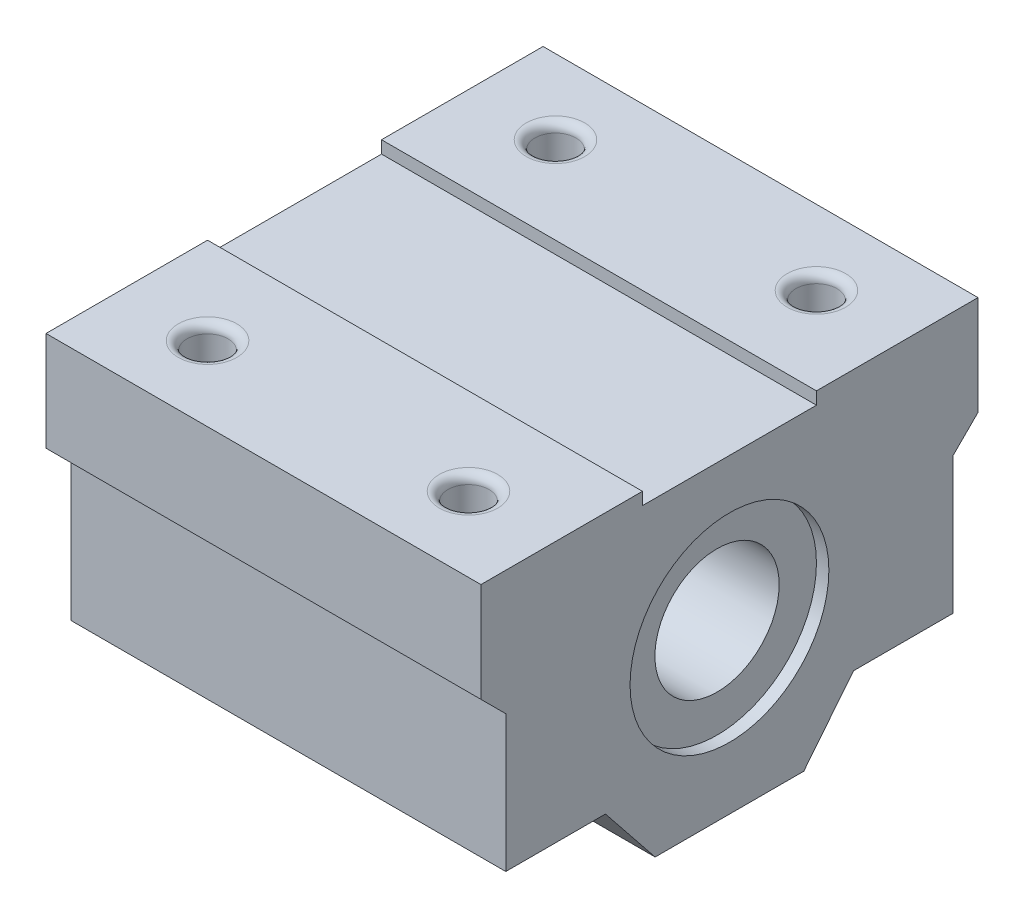
SolidWorks part; units mm, degrees
ref_plane "Front Plane" through (0, 0, 0) normal (0, 0, 1) x (1, 0, 0)
ref_plane "Top Plane" through (0, 0, 0) normal (0, 1, 0) x (1, 0, 0)
ref_plane "Right Plane" through (0, 0, 0) normal (1, 0, 0) x (0, 0, -1)
sketch "Sketch1" plane through (0, 0, 0) normal (1, 0, 0) x (0, 0, -1)
  line L0 (-20, 26) -> (-7, 26)
  line L1 (-5.9801, 0) -> (5.9801, 0)
  line L2 (5.9801, 0) -> (9.9801, 5)
  line L3 (9.9801, 5) -> (18, 5)
  line L4 (18, 5) -> (18, 16)
  line L5 (18, 16) -> (20, 18)
  line L6 (20, 18) -> (20, 26)
  line L7 (0, 0) -> (0, 32.3281) construction
  line L8 (-5.9801, 0) -> (-9.9801, 5)
  line L9 (-9.9801, 5) -> (-18, 5)
  line L10 (-18, 5) -> (-18, 16)
  line L11 (-18, 16) -> (-20, 18)
  line L12 (-20, 18) -> (-20, 26)
  line L17 (-7, 25) -> (7, 25)
  line L18 (-7, 25) -> (-7, 26)
  line L21 (7, 25) -> (7, 26)
  line L22 (7, 26) -> (20, 26)
  dimension "D1" = 40
  dimension "D2" = 20
  dimension "D3" = 26
  dimension "D4" = 21
  dimension "D5" = 2
  dimension "D6" = 2
  dimension "D7" = 8
  dimension "D8" = 4
  dimension "D9" = 8
  dimension "D10" = 21
  dimension "D15" = 1
extrude "Boss-Extrude1" add sketch "Sketch1" along normal mid plane 35
sketch "Sketch2" plane through (17.5, 0, 0) normal (1, 0, 0) x (0, 0, -1)
  line L0 (-18.9525, 22) -> (20.4204, 22) construction
  line L1 (-20, 26) -> (-20, 18) construction
  line L5 (20, 26) -> (7, 26) construction
  circle A0 centre (0, 13) radius 5
  dimension "D2" = 20
  dimension "D1" = 10
  dimension "D3" = 13
extrude "Cut-Extrude1" cut sketch "Sketch2" against normal through all
sketch "Sketch3" plane through (0, 26, 0) normal (0, 1, 0) x (1, 0, 0)
  line L0 (17.5, 20) -> (-17.5, 20) construction
  line L1 (17.5, 20) -> (-17.5, 20) construction
  line L3 (-17.5, 20) -> (-17.5, 7) construction
  circle A0 centre (-10.5, 14) radius 1.65
  circle A1 centre (10.5, 14) radius 1.65
  circle A2 centre (10.5, -14) radius 1.65
  circle A3 centre (-10.5, -14) radius 1.65
  dimension "D5" = 3.3
  dimension "D1" = 28
  dimension "D2" = 6
  dimension "D3" = 6
  dimension "D8" = 7
  dimension "D4" = 28
  dimension "D6" = 21
  dimension "D7" = 21
extrude "Cut-Extrude2" cut sketch "Sketch3" against normal through all
fillet "Fillet1" radius 0.7 4 edges at (-10.5, 26, -12.35) (10.5, 26, -12.35) (10.5, 26, 15.65) (-10.5, 26, 15.65)
sketch "Sketch8" plane through (17.5, 0, 0) normal (1, 0, 0) x (0, 0, -1)
  circle A0 centre (0, 13) radius 8
  dimension "D1" = 16
extrude "Cut-Extrude5" cut sketch "Sketch8" against normal blind 1
mirror "Mirror3" about plane through (0, 0, 0) normal (1, 0, 0) of "Cut-Extrude5"
